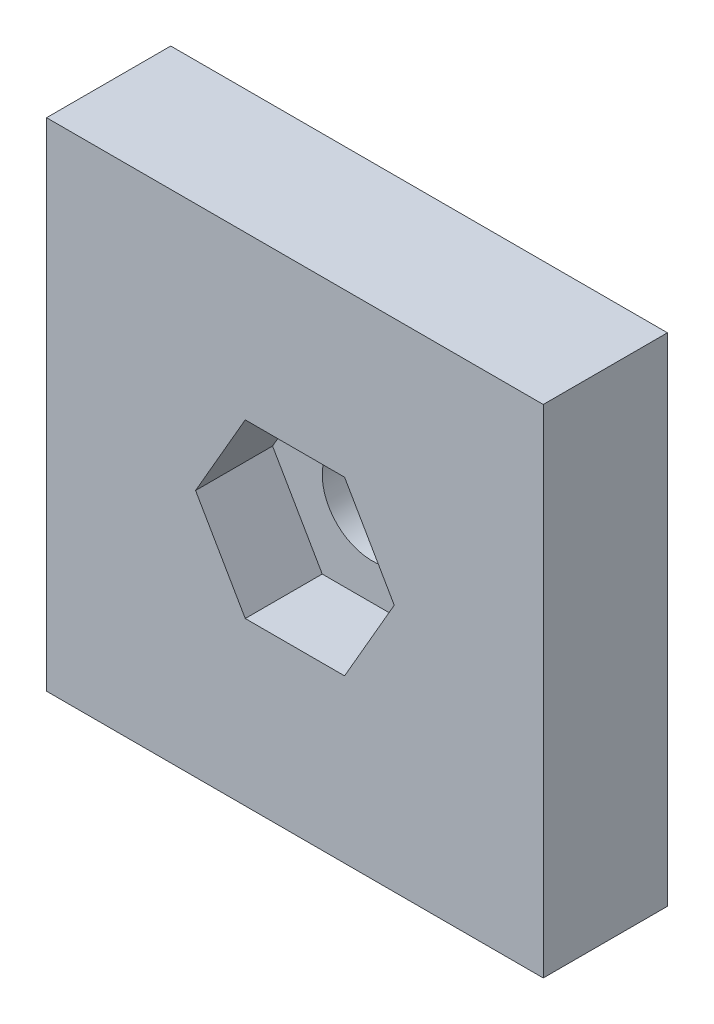
SolidWorks part; units mm, degrees
ref_plane "Front Plane" through (0, 0, 0) normal (0, 0, 1) x (1, 0, 0)
ref_plane "Top Plane" through (0, 0, 0) normal (0, 1, 0) x (1, 0, 0)
ref_plane "Right Plane" through (0, 0, 0) normal (1, 0, 0) x (0, 0, -1)
sketch "Sketch1" plane through (0, 0, 0) normal (0, 0, 1) x (1, 0, 0)
  line L1 (0, 0) -> (-20, 0)
  line L2 (0, 0) -> (0, 20)
  line L3 (0, 20) -> (-20, 20)
  line L4 (-20, 0) -> (-20, 20)
extrude "Boss-Extrude1" add sketch "Sketch1" along normal blind 5
sketch "Sketch2" plane through (0, 0, 5) normal (0, 0, 1) x (1, 0, 0)
  line L0 (-10, 20) -> (-10, -1.6829) construction
  line L1 (0, 20) -> (-20, 20) construction
  line L2 (-20, 20) -> (-20, 0) construction
  line L3 (0, 10) -> (-20, 10) construction
  line L4 (0, 0) -> (0, 20) construction
  line L7 (-6, 10) -> (-8, 13.4641)
  line L8 (-8, 13.4641) -> (-12, 13.4641)
  line L9 (-12, 13.4641) -> (-14, 10)
  line L10 (-14, 10) -> (-12, 6.5359)
  line L11 (-12, 6.5359) -> (-8, 6.5359)
  line L12 (-8, 6.5359) -> (-6, 10)
  circle A1 centre (-10, 10) radius 3.4641 construction
extrude "Cut-Extrude1" cut sketch "Sketch2" against normal blind 3.1
sketch "Sketch4" plane through (0, 0, 5) normal (0, 0, 1) x (1, 0, 0)
  line L0 (-10, 0) -> (-10, 20) construction
  line L1 (-20, 0) -> (0, 0) construction
  line L2 (0, 20) -> (-20, 20) construction
  line L3 (-20, 10) -> (0, 10) construction
  line L4 (-20, 20) -> (-20, 0) construction
  line L5 (0, 0) -> (0, 20) construction
  circle A0 centre (-10, 10) radius 2
extrude "Cut-Extrude2" cut sketch "Sketch4" against normal through all
